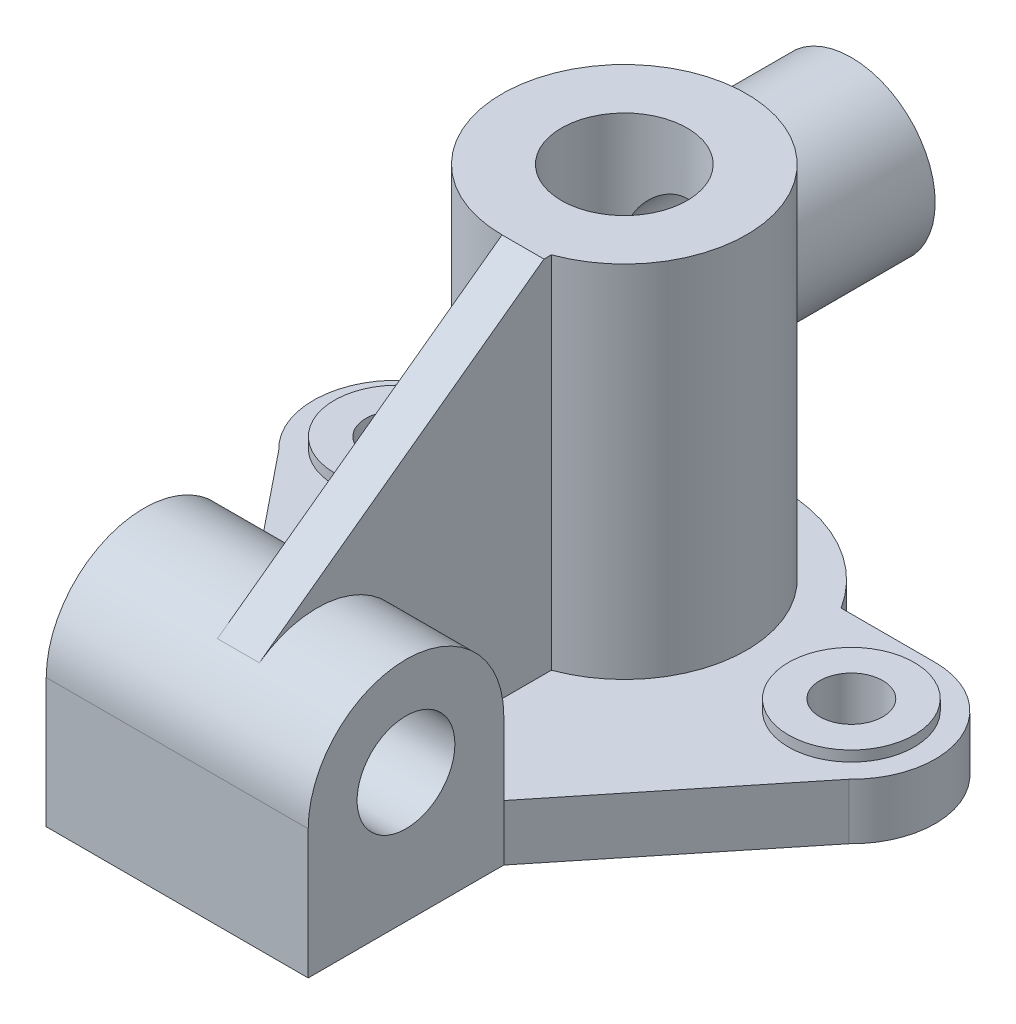
SolidWorks part; units mm, degrees
ref_plane "Alzado" through (0, 0, 0) normal (0, 0, 1) x (1, 0, 0)
ref_plane "Planta" through (0, 0, 0) normal (0, 1, 0) x (1, 0, 0)
ref_plane "Vista lateral" through (0, 0, 0) normal (1, 0, 0) x (0, 0, -1)
sketch "Croquis1" plane through (0, 0, 0) normal (0, 1, 0) x (1, 0, 0)
  line L0 (0, 0) -> (65, 0) construction
  line L1 (0, 65.8003) -> (0, 0) construction
  line L2 (0, 0) -> (0, -86.2531) construction
  line L3 (-37.5, -72) -> (37.5, -72) construction
  line L4 (37.5, -72) -> (81.5959, -17.3372) construction
  line L5 (65, 24) -> (38.0657, 24) construction
  line L6 (-37.5, -72) -> (-81.5959, -17.3372) construction
  line L7 (-65, 24) -> (-38.0657, 24) construction
  circle A0 centre (0, 0) radius 18 construction
  circle A1 centre (0, 0) radius 35 construction
  arc A2 (38.0657, 24) -> (-38.0657, 24) centre (0, 0) ccw construction
  circle A3 centre (65, 0) radius 9 construction
  circle A4 centre (65, 0) radius 18 construction
  arc A5 (81.5959, -17.3372) -> (65, 24) centre (65, 0) ccw construction
  arc A6 (-81.5959, -17.3372) -> (-65, 24) centre (-65, 0) cw construction
  circle A7 centre (-65, 0) radius 18 construction
  circle A8 centre (-65, 0) radius 9 construction
  point P16 (0, -72)
  dimension "D1" = 36
  dimension "D2" = 70
  dimension "D3" = 90
  dimension "D4" = 18
  dimension "D5" = 36
  dimension "D6" = 48
  dimension "D7" = 65
  dimension "D8" = 72
  dimension "D9" = 37.5
sketch "Croquis2" plane through (0, 0, 0) normal (0, 1, 0) x (1, 0, 0)
  line L0 (-65, 24) -> (-38.0657, 24) construction
  line L1 (-37.5, -72) -> (-81.5959, -17.3372) construction
  line L2 (-37.5, -72) -> (37.5, -72) construction
  line L3 (37.5, -72) -> (81.5959, -17.3372) construction
  line L4 (65, 24) -> (38.0657, 24) construction
  line L5 (-65, 24) -> (-38.0657, 24)
  line L6 (-37.5, -72) -> (-81.5959, -17.3372)
  line L7 (-37.5, -72) -> (37.5, -72)
  line L8 (37.5, -72) -> (81.5959, -17.3372)
  line L9 (65, 24) -> (38.0657, 24)
  circle A0 centre (0, 0) radius 18 construction
  circle A1 centre (65, 0) radius 9 construction
  circle A2 centre (-65, 0) radius 9 construction
  arc A3 (-65, 24) -> (-81.5959, -17.3372) centre (-65, 0) ccw construction
  arc A4 (81.5959, -17.3372) -> (65, 24) centre (65, 0) ccw construction
  arc A5 (38.0657, 24) -> (-38.0657, 24) centre (0, 0) ccw construction
  circle A6 centre (0, 0) radius 18
  circle A7 centre (65, 0) radius 9
  circle A8 centre (-65, 0) radius 9
  arc A9 (-65, 24) -> (-81.5959, -17.3372) centre (-65, 0) ccw
  arc A10 (81.5959, -17.3372) -> (65, 24) centre (65, 0) ccw
  arc A11 (38.0657, 24) -> (-38.0657, 24) centre (0, 0) ccw
extrude "Saliente-Extruir1" add sketch "Croquis2" along normal blind 16
sketch "Croquis3" plane through (0, 0, 0) normal (0, 1, 0) x (1, 0, 0)
  circle A0 centre (65, 0) radius 18 construction
  circle A1 centre (65, 0) radius 9 construction
  circle A2 centre (-65, 0) radius 18 construction
  circle A3 centre (-65, 0) radius 9 construction
  circle A4 centre (65, 0) radius 18
  circle A5 centre (65, 0) radius 9
  circle A6 centre (-65, 0) radius 18
  circle A7 centre (-65, 0) radius 9
extrude "Saliente-Extruir2" add sketch "Croquis3" along normal blind 19
sketch "Croquis4" plane through (0, 0, 0) normal (0, 1, 0) x (1, 0, 0)
  circle A0 centre (0, 0) radius 35 construction
  circle A1 centre (0, 0) radius 18 construction
  circle A2 centre (0, 0) radius 35
  circle A3 centre (0, 0) radius 18
extrude "Saliente-Extruir3" add sketch "Croquis4" along normal blind 119
sketch "Croquis5" plane through (0, 0, 0) normal (1, 0, 0) x (0, 0, -1)
  line L0 (-72, 0) -> (-72, 37)
  line L1 (-128, 37) -> (-128, 0)
  line L2 (-128, 0) -> (-72, 0)
  arc A0 (-72, 37) -> (-128, 37) centre (-100, 37) ccw
  circle A1 centre (-100, 37) radius 14
  dimension "D1" = 28
  dimension "D2" = 28
  dimension "D3" = 37
extrude "Saliente-Extruir4" add sketch "Croquis5" along normal mid plane 75
sketch "Croquis6" plane through (0, 0, 0) normal (1, 0, 0) x (0, 0, -1)
  line L0 (-72, 16) -> (-18, 16)
  line L1 (-72, 16) -> (-17.3372, 16) construction
  line L2 (-18, 16) -> (-18, 119)
  line L3 (35, 119) -> (-35, 119) construction
  line L4 (-18, 119) -> (-35, 119)
  line L5 (-35, 119) -> (-116.4879, 59.6307)
  line L6 (-72, 37) -> (-72, 16)
  arc A0 (-72, 37) -> (-128, 37) centre (-100, 37) ccw construction
  arc A1 (-116.4879, 59.6307) -> (-72, 37) centre (-100, 37) cw
  dimension "D1" = 28
  dimension "D2" = 17
extrude "Saliente-Extruir5" add sketch "Croquis6" along normal blind 12
ref_plane "Plano1" through (0, 0, -65) normal (0, 0, 1) x (1, 0, 0)
sketch "Croquis7" plane through (0, 0, -65) normal (0, 0, 1) x (1, 0, 0)
  line L0 (0, 0) -> (0, 131.559) construction
  circle A0 centre (0, 89) radius 12.5
  circle A1 centre (0, 89) radius 24
  dimension "D1" = 25
  dimension "D2" = 48
  dimension "D3" = 30
extrude "Saliente-Extruir6" add sketch "Croquis7" along normal up to next
sketch "Croquis8" plane through (0, 0, -65) normal (0, 0, 1) x (1, 0, 0)
  circle A0 centre (0, 89) radius 12.5
  dimension "D1" = 25
extrude "Cortar-Extruir1" cut sketch "Croquis8" along normal up to surface (52.0481 mm away)
